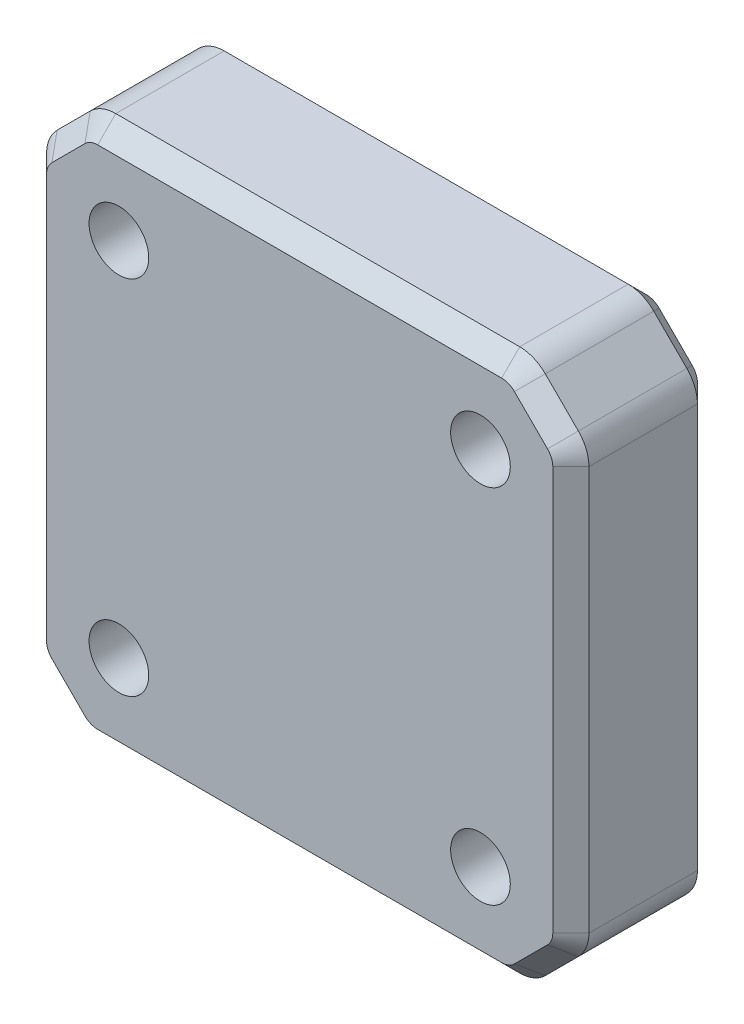
SolidWorks part; units mm, degrees
ref_plane "正面" through (0, 0, 0) normal (0, 0, 1) x (1, 0, 0)
ref_plane "平面" through (0, 0, 0) normal (0, 1, 0) x (1, 0, 0)
ref_plane "右側面" through (0, 0, 0) normal (1, 0, 0) x (0, 0, -1)
sketch "ｽｹｯﾁ1" plane through (0, 0, 0) normal (0, 0, 1) x (1, 0, 0)
  line L1 (15, -15) -> (-15, -15)
  line L2 (15, -15) -> (15, 15)
  line L3 (15, 15) -> (-15, 15)
  line L4 (-15, -15) -> (-15, 15)
  line L5 (15, -15) -> (-15, 15) construction
  line L6 (15, 15) -> (-15, -15) construction
  point P0 (0, 0)
  dimension "D1" = 30
  dimension "D2" = 30
extrude "ﾎﾞｽ - 押し出し1" add sketch "ｽｹｯﾁ1" along normal blind 8
sketch "ｽｹｯﾁ2" plane through (0, 0, 8) normal (0, 0, 1) x (1, 0, 0)
  line L1 (10, -10) -> (-10, -10)
  line L2 (10, -10) -> (10, 10)
  line L3 (10, 10) -> (-10, 10)
  line L4 (-10, -10) -> (-10, 10)
  line L5 (10, -10) -> (-10, 10) construction
  line L6 (10, 10) -> (-10, -10) construction
  point P0 (0, 0)
  dimension "D1" = 20
  dimension "D2" = 20
hole_wizard "M4 すきま穴1" positions "ｽｹｯﾁ3" profile "ｽｹｯﾁ4" hole size "M4" standard "ISO" end condition through all
sketch "ｽｹｯﾁ3" plane through (0, 0, 8) normal (0, 0, 1) x (1, 0, 0)
  point P0 (-10, 10)
  point P3 (-10, -10)
  point P6 (10, -10)
  point P9 (10, 10)
sketch "ｽｹｯﾁ4" plane through (-10, 10, 8) normal (1, 0, 0) x (0, -1, 0)
  line L0 (0, 0) -> (0, 8)
  line L1 (0, 8) -> (1.65, 8)
  line L2 (1.65, 8) -> (1.65, 0)
  line L5 (1.65, 0) -> (0, 0)
  line L11 (0, -6.35) -> (0, 107.95) construction
  dimension "通し穴の直径" = 3.3
  dimension "通し穴の深さ" = 8
chamfer "面取り1" distance 3 angle 45 4 edges at (15, 15, 4) (-15, 15, 4) (15, -15, 4) (-15, -15, 4)
fillet "ﾌｨﾚｯﾄ1" radius 2 8 edges at (15, 12, 4) (12, 15, 4) (-12, 15, 4) (-15, 12, 4) (-15, -12, 4) (-12, -15, 4) (15, -12, 4) (12, -15, 4)
chamfer "面取り2" distance 1 angle 45 32 edges at (15, 0, 0) (14.8478, 11.9369, 0) (14.8478, -11.9369, 0) (13.5, 13.5, 0) (13.5, -13.5, 0) (11.9369, 14.8478, 0) (11.9369, -14.8478, 0) (0, 15, 0) (0, -15, 0) (-11.9369, 14.8478, 0) (-11.9369, -14.8478, 0) (-13.5, 13.5, 0) (-13.5, -13.5, 0) (-14.8478, 11.9369, 0) (-14.8478, -11.9369, 0) (-15, 0, 0) (0, -15, 8) (11.9369, -14.8478, 8) (-11.9369, -14.8478, 8) (13.5, -13.5, 8) (-13.5, -13.5, 8) (14.8478, -11.9369, 8) (-14.8478, -11.9369, 8) (15, 0, 8) (-15, 0, 8) (14.8478, 11.9369, 8) (-14.8478, 11.9369, 8) (13.5, 13.5, 8) (-13.5, 13.5, 8) (11.9369, 14.8478, 8) (-11.9369, 14.8478, 8) (0, 15, 8)
